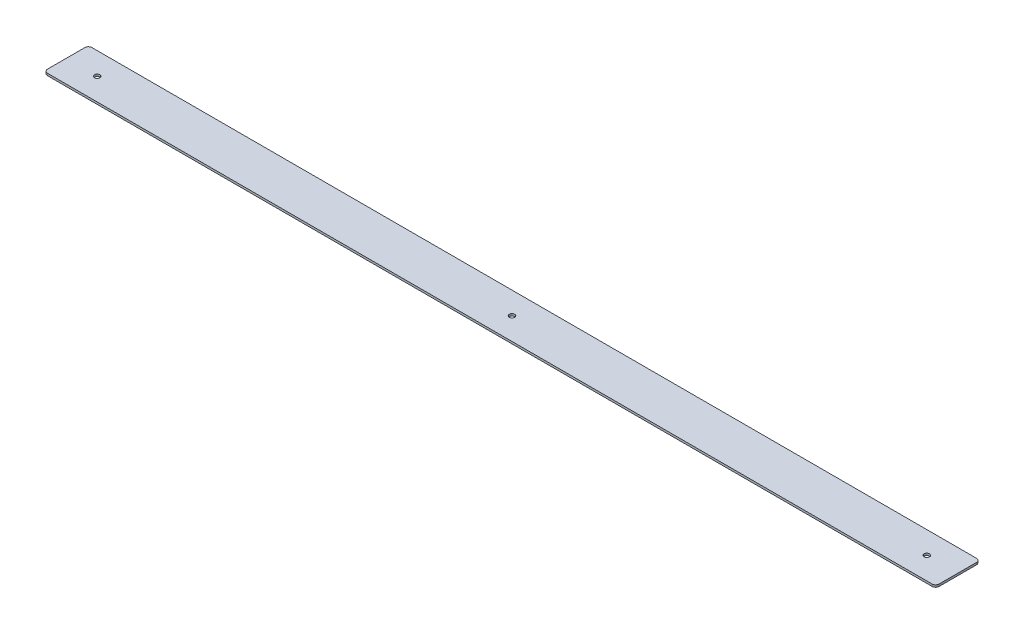
SolidWorks part; units mm, degrees
ref_plane "Front Plane" through (0, 0, 0) normal (0, 0, 1) x (1, 0, 0)
ref_plane "Top Plane" through (0, 0, 0) normal (0, 1, 0) x (1, 0, 0)
ref_plane "Right Plane" through (0, 0, 0) normal (1, 0, 0) x (0, 0, -1)
sketch "Sketch1" plane through (0, 0, 0) normal (0, 1, 0) x (1, 0, 0)
  line L1 (-318.2832, -15.875) -> (318.2832, -15.875)
  line L2 (-318.2832, -15.875) -> (-318.2832, 15.875)
  line L3 (-318.2832, 15.875) -> (318.2832, 15.875)
  line L4 (318.2832, -15.875) -> (318.2832, 15.875)
  line L5 (-318.2832, -15.875) -> (318.2832, 15.875) construction
  line L6 (-318.2832, 15.875) -> (318.2832, -15.875) construction
  point P0 (0, 0)
  dimension "D1" = 31.75
  dimension "D2" = 636.5663
extrude "Boss-Extrude1" add sketch "Sketch1" along normal blind 1.524
sketch "Sketch2" plane through (0, 1.524, 0) normal (0, 1, 0) x (1, 0, 0)
  line L0 (-318.2832, 15.875) -> (318.2832, -15.875) construction
  line L1 (-296.164, 0) -> (296.164, 0) construction
  circle A0 centre (-296.164, 0) radius 1.905
  circle A1 centre (296.164, 0) radius 1.905
  circle A2 centre (0, 0) radius 1.905
  point P8 (0, 0)
  dimension "D2" = 3.81
  dimension "D1" = 592.328
extrude "Cut-Extrude1" cut sketch "Sketch2" against normal through all
fillet "Fillet1" radius 2.54 4 edges at (318.2832, 0.762, 15.875) (318.2832, 0.762, -15.875) (-318.2832, 0.762, 15.875) (-318.2832, 0.762, -15.875)
